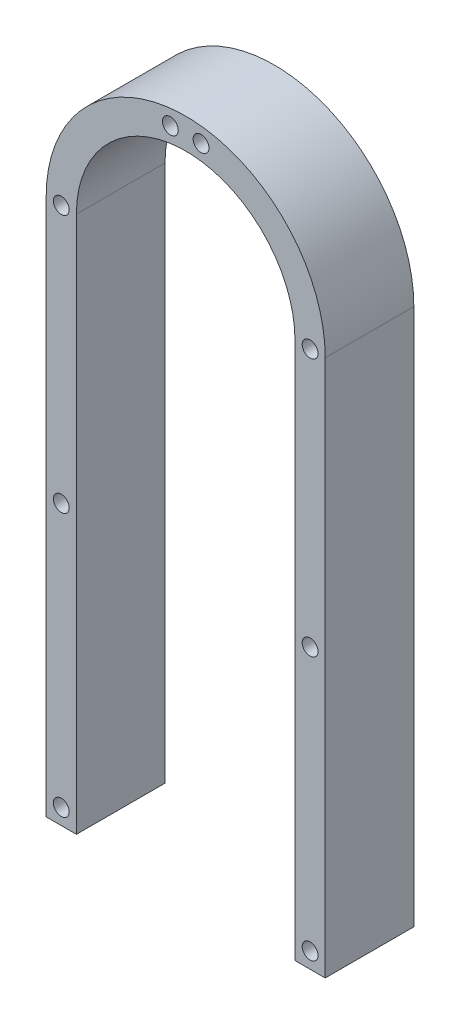
SolidWorks part; units mm, degrees
ref_plane "Front Plane" through (0, 0, 0) normal (0, 0, 1) x (1, 0, 0)
ref_plane "Top Plane" through (0, 0, 0) normal (0, 1, 0) x (1, 0, 0)
ref_plane "Right Plane" through (0, 0, 0) normal (1, 0, 0) x (0, 0, -1)
sketch "Sketch1" plane through (0, 0, 0) normal (0, 0, 1) x (1, 0, 0)
  line L0 (-179.0854, -18.7892) -> (-179.0854, 212.1883)
  line L1 (-119.0854, -18.7892) -> (-119.0854, 212.1883)
  line L2 (-172.5854, -18.7892) -> (-172.5854, 212.1883)
  line L3 (-125.5854, -18.7892) -> (-125.5854, 212.1883)
  arc A0 (-119.0854, 212.1883) -> (-179.0854, 212.1883) centre (-149.0854, 212.1883) ccw
  arc A1 (-179.0854, -18.7892) -> (-119.0854, -18.7892) centre (-149.0854, -18.7892) ccw
  arc A2 (-125.5854, 212.1883) -> (-172.5854, 212.1883) centre (-149.0854, 212.1883) ccw
  arc A3 (-172.5854, -18.7892) -> (-125.5854, -18.7892) centre (-149.0854, -18.7892) ccw
  dimension "D1" = 47
  dimension "D2" = 47
  dimension "D3" = 53.5
extrude "Boss-Extrude1" add sketch "Sketch1" along normal blind 19.05
sketch "Sketch2" plane through (0, 0, 19.05) normal (0, 0, 1) x (1, 0, 0)
  line L0 (-175.8354, 212.1883) -> (-175.8354, -18.7892) construction
  line L1 (-122.3354, 212.1883) -> (-122.3354, -18.7892) construction
  line L2 (-149.0854, 242.1883) -> (-149.0854, 231.9427) construction
  line L3 (-149.0854, -48.7892) -> (-149.0854, -37.4384) construction
  line L4 (-179.0854, 96.6996) -> (-118.7003, 96.6996) construction
  line L5 (-179.0854, 212.1883) -> (-179.0854, -18.7892) construction
  arc A0 (-122.3354, 212.1883) -> (-175.8354, 212.1883) centre (-149.0854, 212.1883) ccw construction
  arc A1 (-119.0854, 212.1883) -> (-179.0854, 212.1883) centre (-149.0854, 212.1883) ccw construction
  arc A2 (-125.5854, 212.1883) -> (-172.5854, 212.1883) centre (-149.0854, 212.1883) ccw construction
  arc A3 (-175.8354, -18.7892) -> (-122.3354, -18.7892) centre (-149.0854, -18.7892) ccw construction
  arc A4 (-179.0854, -18.7892) -> (-119.0854, -18.7892) centre (-149.0854, -18.7892) ccw construction
  circle A5 centre (-145.7854, 238.734) radius 1.7
  circle A7 centre (-122.3354, 212.1883) radius 1.7
  circle A8 centre (-152.4854, -45.3222) radius 1.7
  circle A9 centre (-168.0005, -37.7043) radius 1.7
  circle A10 centre (-175.8354, -18.7892) radius 1.7
  circle A11 centre (-175.8354, 212.1883) radius 1.7
  circle A13 centre (-145.6854, -45.3222) radius 1.7
  circle A14 centre (-175.8354, 100.0996) radius 1.7
  circle A15 centre (-175.8354, 93.2996) radius 1.7
  circle A16 centre (-122.3354, 100.0996) radius 1.7
  circle A17 centre (-122.3354, 93.2996) radius 1.7
  circle A19 centre (-122.3354, -18.7892) radius 1.7
  circle A20 centre (-130.1703, -37.7043) radius 1.7
  circle A25 centre (-175.8354, 156.6996) radius 1.7
  circle A26 centre (-122.3354, 156.6996) radius 1.7
  circle A29 centre (-175.8354, 66.6996) radius 1.7
  circle A30 centre (-122.3354, 66.6996) radius 1.7
  circle A31 centre (-175.8354, 36.6996) radius 1.7
  circle A32 centre (-122.3354, 36.6996) radius 1.7
  circle A33 centre (-175.8354, 6.6996) radius 1.7
  circle A34 centre (-122.3354, 6.6996) radius 1.7
  circle A35 centre (-152.3854, 238.734) radius 1.7
  point P35 (-149.0854, 212.1883)
  point P52 (-149.0854, -18.7892)
  dimension "D1" = 3.25
  dimension "D2" = 3.25
  dimension "D3" = 3.25
  dimension "D4" = 3.4
  dimension "D6" = 3.4
  dimension "D8" = 3.4
  dimension "D9" = 3.4
  dimension "D5" = 3.4
  dimension "D12" = 3.3
  dimension "D13" = 3.3
  dimension "D14" = 3.4
  dimension "D7" = 3.4
  dimension "D16" = 3.4
  dimension "D17" = 3.4
  dimension "D18" = 3.4
  dimension "D19" = 3.4
  dimension "D20" = 3.4
  dimension "D10" = 3.4
  dimension "D11" = 3.4
  dimension "D21" = 3.4
  dimension "D22" = 3.4
  dimension "D25" = 3.4
  dimension "D26" = 3.4
  dimension "D15" = 3.4
  dimension "D23" = 3.4
extrude "Cut-Extrude1" cut sketch "Sketch2" against normal through all
sketch "Sketch3" plane through (0, 0, 19.05) normal (0, 0, 1) x (1, 0, 0)
  line L1 (-149.0854, 96.6996) -> (-100.1673, 96.6996)
  line L2 (-100.1673, 96.6996) -> (-100.1673, -59.1719)
  line L3 (-100.1673, -59.1719) -> (-212.5278, -59.1719)
  line L4 (-212.5278, -59.1719) -> (-212.5278, 96.6996)
  line L5 (-149.0854, 96.6996) -> (-212.5278, 96.6996)
extrude "Cut-Extrude2" cut sketch "Sketch3" against normal through all
